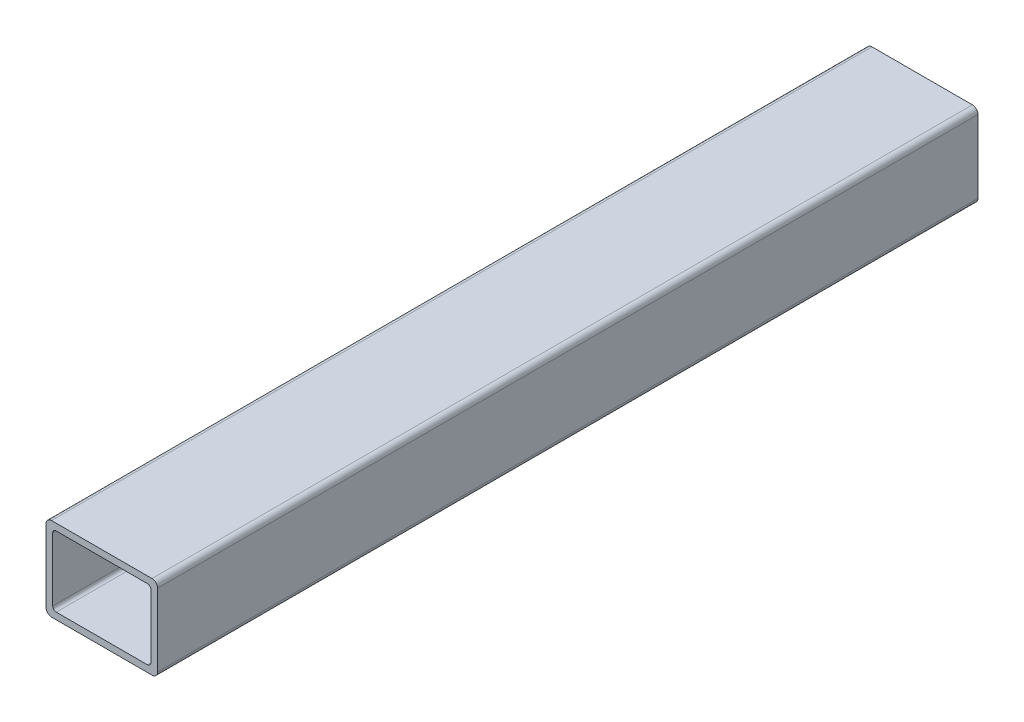
SolidWorks part; units mm, degrees
material "Plain Carbon Steel"
ref_plane "Front" through (0, 0, 0) normal (0, 0, 1) x (1, 0, 0)
ref_plane "Top" through (0, 0, 0) normal (0, 1, 0) x (1, 0, 0)
ref_plane "Right" through (0, 0, 0) normal (1, 0, 0) x (0, 0, -1)
sketch "Sketch1" plane through (0, 0, 0) normal (0, 0, 1) x (1, 0, 0)
  line L0 (-22.352, 0) -> (-25.4, 0) construction
  line L1 (22.86, -19.05) -> (-22.86, -19.05)
  line L2 (25.4, -16.51) -> (25.4, 16.51)
  line L3 (22.86, 19.05) -> (-22.86, 19.05)
  line L4 (-25.4, -16.51) -> (-25.4, 16.51)
  line L5 (25.4, -19.05) -> (-25.4, 19.05) construction
  line L6 (25.4, 19.05) -> (-25.4, -19.05) construction
  line L7 (20.7518, 16.002) -> (-20.7518, 16.002)
  line L8 (22.352, 14.4018) -> (22.352, -14.4018)
  line L9 (20.7518, -16.002) -> (-20.7518, -16.002)
  line L10 (-22.352, 14.4018) -> (-22.352, -14.4018)
  line L11 (22.352, 16.002) -> (-22.352, -16.002) construction
  line L12 (22.352, -16.002) -> (-22.352, 16.002) construction
  line L13 (0, -16.002) -> (0, -19.05) construction
  line L14 (22.352, -14.4018) -> (22.352, -19.05) construction
  line L16 (22.352, -19.05) -> (25.4, -19.05) construction
  arc A0 (-20.7518, -16.002) -> (-22.352, -14.4018) centre (-20.7518, -14.4018) cw
  arc A1 (22.352, -14.4018) -> (20.7518, -16.002) centre (20.7518, -14.4018) cw
  arc A2 (20.7518, 16.002) -> (22.352, 14.4018) centre (20.7518, 14.4018) cw
  arc A3 (-20.7518, 16.002) -> (-22.352, 14.4018) centre (-20.7518, 14.4018) ccw
  arc A4 (22.86, -19.05) -> (25.4, -16.51) centre (22.86, -16.51) ccw
  arc A5 (25.4, 16.51) -> (22.86, 19.05) centre (22.86, 16.51) ccw
  arc A6 (-22.86, 19.05) -> (-25.4, 16.51) centre (-22.86, 16.51) ccw
  arc A7 (-22.86, -19.05) -> (-25.4, -16.51) centre (-22.86, -16.51) cw
  point P0 (0, 0)
  point P6 (0, 0)
  dimension "D2" = 1.6002
  dimension "D3" = 2.54
sketch "Sketch2" plane through (0, 0, 0) normal (1, 0, 0) x (0, 0, -1)
  line L0 (-152.4, 0) -> (152.4, 0) construction
  dimension "Length" = 304.8
ref_plane "Plane1" through (25.4, 0, 0) normal (1, 0, 0) x (0, 0, -1)
sketch "Sketch5" plane through (25.4, 0, 0) normal (1, 0, 0) x (0, 0, -1)
  line L0 (-152.4, 19.05) -> (-152.4, -19.05) construction
  line L1 (152.4, 19.05) -> (152.4, -19.05) construction
sketch "Sketch4" plane through (0, 0, 0) normal (0, 0, 1) x (1, 0, 0)
  line L0 (25.4, -16.51) -> (25.4, 16.51) construction
  line L1 (22.86, 19.05) -> (-22.86, 19.05) construction
  line L2 (-25.4, -16.51) -> (-25.4, 16.51) construction
  line L3 (22.86, -19.05) -> (-22.86, -19.05) construction
  line L4 (22.352, 14.4018) -> (22.352, -14.4018) construction
  line L5 (20.7518, -16.002) -> (-20.7518, -16.002) construction
  line L6 (-22.352, 14.4018) -> (-22.352, -14.4018) construction
  line L7 (20.7518, 16.002) -> (-20.7518, 16.002) construction
  line L8 (25.4, -16.51) -> (25.4, 16.51)
  line L9 (22.86, 19.05) -> (-22.86, 19.05)
  line L10 (-25.4, -16.51) -> (-25.4, 16.51)
  line L11 (22.86, -19.05) -> (-22.86, -19.05)
  line L12 (22.352, 14.4018) -> (22.352, -14.4018)
  line L13 (20.7518, -16.002) -> (-20.7518, -16.002)
  line L14 (-22.352, 14.4018) -> (-22.352, -14.4018)
  line L15 (20.7518, 16.002) -> (-20.7518, 16.002)
  arc A0 (25.4, 16.51) -> (22.86, 19.05) centre (22.86, 16.51) ccw construction
  arc A1 (-22.86, 19.05) -> (-25.4, 16.51) centre (-22.86, 16.51) ccw construction
  arc A2 (-25.4, -16.51) -> (-22.86, -19.05) centre (-22.86, -16.51) ccw construction
  arc A3 (22.86, -19.05) -> (25.4, -16.51) centre (22.86, -16.51) ccw construction
  arc A4 (20.7518, -16.002) -> (22.352, -14.4018) centre (20.7518, -14.4018) ccw construction
  arc A5 (-22.352, -14.4018) -> (-20.7518, -16.002) centre (-20.7518, -14.4018) ccw construction
  arc A6 (-20.7518, 16.002) -> (-22.352, 14.4018) centre (-20.7518, 14.4018) ccw construction
  arc A7 (22.352, 14.4018) -> (20.7518, 16.002) centre (20.7518, 14.4018) ccw construction
  arc A8 (25.4, 16.51) -> (22.86, 19.05) centre (22.86, 16.51) ccw
  arc A9 (-22.86, 19.05) -> (-25.4, 16.51) centre (-22.86, 16.51) ccw
  arc A10 (-25.4, -16.51) -> (-22.86, -19.05) centre (-22.86, -16.51) ccw
  arc A11 (22.86, -19.05) -> (25.4, -16.51) centre (22.86, -16.51) ccw
  arc A12 (20.7518, -16.002) -> (22.352, -14.4018) centre (20.7518, -14.4018) ccw
  arc A13 (-22.352, -14.4018) -> (-20.7518, -16.002) centre (-20.7518, -14.4018) ccw
  arc A14 (-20.7518, 16.002) -> (-22.352, 14.4018) centre (-20.7518, 14.4018) ccw
  arc A15 (22.352, 14.4018) -> (20.7518, 16.002) centre (20.7518, 14.4018) ccw
extrude "Boss-Extrude1" add sketch "Sketch4" along normal blind 373.6137
sketch "Sketch6" plane through (0, 19.05, 0) normal (0, 1, 0) x (1, 0, 0)
  line L0 (0, -373.6137) -> (0, -256.6568) construction
  line L2 (-22.86, -256.6568) -> (22.86, -256.6568) construction
  line L3 (-22.86, 0) -> (-22.86, -373.6137) construction
  line L4 (22.86, 0) -> (22.86, -373.6137) construction
  line L5 (-22.86, -116.9568) -> (22.86, -116.9568) construction
  line L6 (22.86, -373.6137) -> (-22.86, -373.6137) construction
  line L7 (0, -256.6568) -> (0, -116.9568) construction
  line L8 (0, -116.9568) -> (0, 0) construction
  line L9 (22.86, 0) -> (-22.86, 0) construction
  dimension "D1" = 139.7
equation "\"D3@Sketch1\"=\"Outside Width@Sketch1\"*.05"
equation "\"D2@Sketch1\"=\"D1@Sketch1\"*.05"
